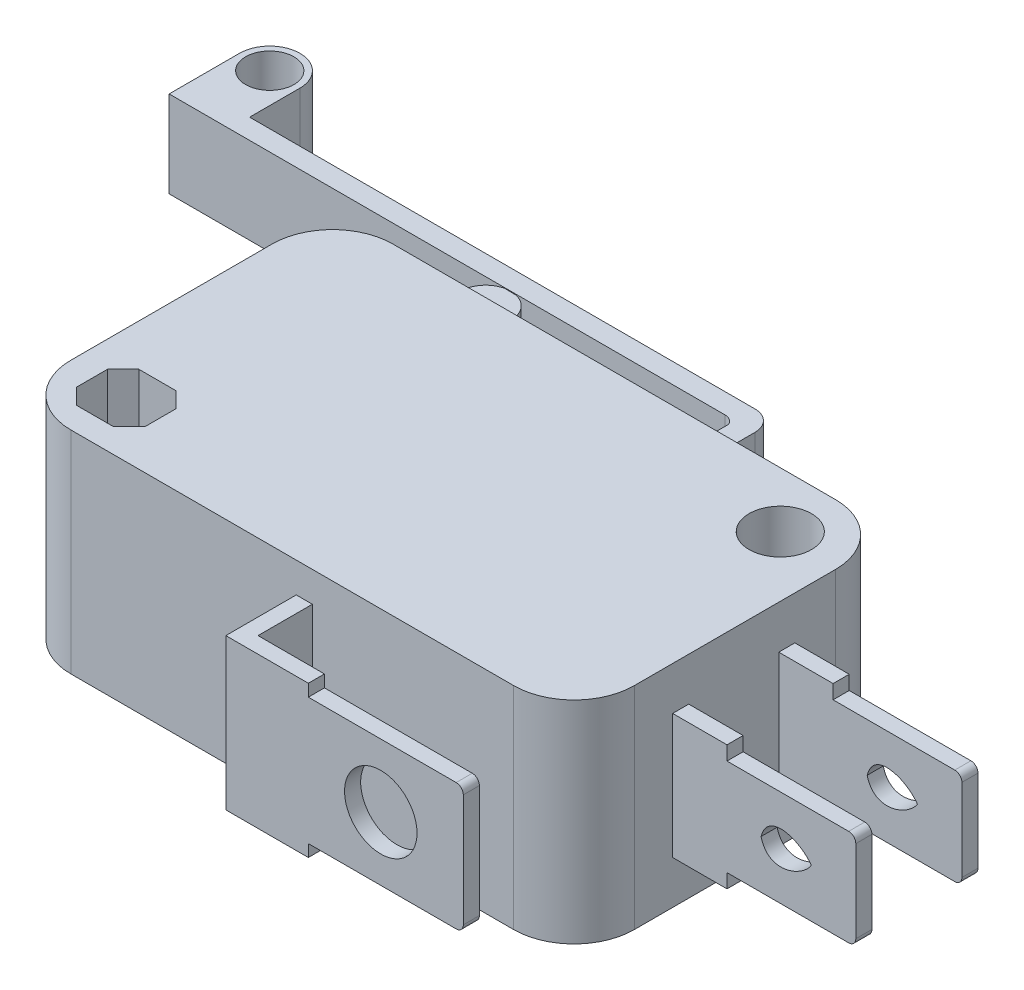
SolidWorks part; units mm, degrees
ref_plane "Alzado" through (0, 0, 0) normal (0, 0, 1) x (1, 0, 0)
ref_plane "Planta" through (0, 0, 0) normal (0, 1, 0) x (1, 0, 0)
ref_plane "Vista lateral" through (0, 0, 0) normal (1, 0, 0) x (0, 0, -1)
sketch "Croquis1" plane through (0, 0, 0) normal (0, 1, 0) x (1, 0, 0)
  line L0 (3, 0) -> (25, 0)
  line L1 (0, 3) -> (0, 13)
  line L2 (1.3, 3.525) -> (2.075, 4.3)
  line L3 (4.7, 3.525) -> (3.925, 4.3)
  line L4 (1.3, 1.975) -> (2.075, 1.2)
  line L5 (1.3, 2.75) -> (1.3, 3.525)
  line L6 (2.075, 4.3) -> (3.925, 4.3)
  line L7 (4.7, 3.525) -> (4.7, 1.975)
  line L8 (3.925, 1.2) -> (2.075, 1.2)
  line L9 (1.3, 1.975) -> (1.3, 2.75)
  line L10 (3.925, 1.2) -> (4.7, 1.975)
  line L13 (3, 16) -> (25, 16)
  line L15 (28, 13) -> (28, 3)
  arc A0 (0, 3) -> (3, 0) centre (3, 3) ccw
  circle A1 centre (25, 13.25) radius 1.55
  arc A2 (28, 13) -> (25, 16) centre (25, 13) ccw
  arc A3 (3, 16) -> (0, 13) centre (3, 13) ccw
  arc A4 (25, 0) -> (28, 3) centre (25, 3) ccw
extrude "Saliente-Extruir1" add sketch "Croquis1" along normal blind 10.5
sketch3d "Croquis3D1" plane through (0, 0, 0) normal (0, 0, 1) x (1, 0, 0)
  dimension "D1" = 3.1
sketch "Croquis2" plane through (0, 3.1, 0) normal (0, 1, 0) x (1, 0, 0)
  line L0 (-12.1172, 20) -> (15.5028, 20)
  line L1 (25, 16) -> (3, 16) construction
  line L2 (17, 16) -> (17, 20)
  line L3 (16, 21) -> (-9.1172, 21)
  line L5 (-12.1172, 21) -> (-12.1172, 20)
  line L9 (17, 16) -> (16, 16)
  line L10 (16, 16) -> (16, 19.6904)
  line L12 (-12.1172, 21) -> (-12.1172, 23.5)
  line L14 (-9.1172, 23.5) -> (-9.1172, 21)
  arc A0 (17, 20) -> (16, 21) centre (16, 20) ccw
  arc A1 (15.5028, 20) -> (16, 19.6904) centre (15.5028, 19.4459) cw
  arc A2 (-12.1172, 23.5) -> (-9.1172, 23.5) centre (-10.6172, 23.5) cw
  circle A3 centre (-10.6172, 23.5) radius 1.2
extrude "Saliente-Extruir2" add sketch "Croquis2" along normal blind 4.3
sketch "Croquis3" plane through (0, 3.1, 0) normal (0, 1, 0) x (1, 0, 0)
  line L0 (4.5799, 19.9682) -> (5.1781, 19.9589)
  line L1 (25, 16) -> (3, 16) construction
  line L3 (6.1101, 18.75) -> (6.1101, 16)
  line L4 (6.1101, 16) -> (3.6101, 16)
  line L5 (3.6101, 16) -> (3.6101, 18.75)
  arc A0 (3.6101, 18.75) -> (4.5799, 19.9682) centre (4.8601, 18.75) cw
  arc A1 (5.1781, 19.9589) -> (6.1101, 18.75) centre (4.8601, 18.75) cw
extrude "Saliente-Extruir6" add sketch "Croquis3" along normal blind 4.3
sketch3d "Croquis3D2" plane through (0, 0, 0) normal (0, 0, 1) x (1, 0, 0)
  dimension "D1" = 1.5
sketch "Croquis4" plane through (0, 1.5, 0) normal (0, 1, 0) x (1, 0, 0)
  line L1 (3, 0) -> (25, 0) construction
  line L2 (15, 0) -> (15, -2.7)
  line L3 (15, -3.5) -> (26, -3.5)
  line L4 (15, -3.5) -> (14.2, -3.5)
  line L5 (14.2, -3.5) -> (14.2, 0)
  line L6 (14.2, 0) -> (15, 0)
  line L7 (26, -3.5) -> (26, -2.7)
  line L8 (26, -2.7) -> (15, -2.7)
extrude "Saliente-Extruir7" add sketch "Croquis4" along normal blind 7.5
sketch "Croquis5" plane through (0, 0, 3.5) normal (0, 0, 1) x (1, 0, 0)
  line L0 (26, 1.5) -> (18.3, 1.5)
  line L1 (18.3, 1.5) -> (18.3, 2.1)
  line L2 (18.3, 2.1) -> (25.6464, 2.1)
  line L4 (26, 2.4536) -> (26, 8.0464)
  line L5 (25.6464, 8.4) -> (18.3, 8.4)
  line L6 (18.3, 8.4) -> (18.3, 9)
  line L7 (14.2, 9) -> (26, 9) construction
  line L8 (18.3, 9) -> (27.2932, 9)
  line L9 (27.2932, 9) -> (27.2932, 1.5)
  line L10 (27.2932, 1.5) -> (26, 1.5)
  arc A0 (25.6464, 2.1) -> (26, 2.4536) centre (25.6464, 2.4536) ccw
  arc A1 (26, 8.0464) -> (25.6464, 8.4) centre (25.6464, 8.0464) ccw
  circle A2 centre (21.9, 5.25) radius 1.8
extrude "Cortar-Extruir1" cut sketch "Croquis5" against normal blind 1.5
sketch3d "Croquis3D3" plane through (0, 0, 0) normal (0, 0, 1) x (1, 0, 0)
  dimension "D1" = 2.15
sketch "Croquis6" plane through (0, 2.15, 0) normal (0, 1, 0) x (1, 0, 0)
  line L0 (28, 10.974) -> (37.1, 10.974)
  line L1 (28, 3) -> (28, 13) construction
  line L2 (37.1, 10.974) -> (37.1, 10.174)
  line L3 (37.1, 10.174) -> (28, 10.174)
  line L4 (28, 10.174) -> (28, 10.974)
  line L5 (28, 5.7016) -> (37.1, 5.7016)
  line L6 (37.1, 5.7016) -> (37.1, 4.9016)
  line L7 (37.1, 4.9016) -> (28, 4.9016)
  line L8 (28, 4.9016) -> (28, 5.7016)
extrude "Saliente-Extruir8" add sketch "Croquis6" along normal blind 6.2
sketch "Croquis7" plane through (0, 0, -10.974) normal (0, 0, -1) x (-1, 0, 0)
  line L0 (-37.1, 2.15) -> (-30.7, 2.15)
  line L2 (-37.1, 2.15) -> (-28, 2.15) construction
  line L3 (-30.7, 2.15) -> (-30.7, 2.85)
  line L4 (-30.7, 2.85) -> (-36.7464, 2.85)
  line L6 (-37.1, 3.2036) -> (-37.1, 7.2964)
  line L7 (-36.7464, 7.65) -> (-30.7, 7.65)
  line L8 (-30.7, 7.65) -> (-30.7, 8.35)
  line L9 (-37.1, 8.35) -> (-28, 8.35) construction
  line L10 (-30.7, 8.35) -> (-37.1, 8.35)
  line L11 (-37.1, 8.35) -> (-38.5965, 8.35)
  line L12 (-38.5965, 8.35) -> (-38.5965, 2.85)
  line L13 (-38.5965, 2.85) -> (-38.5965, 2.15)
  line L14 (-38.5965, 2.15) -> (-37.1, 2.15)
  arc A0 (-36.7464, 7.65) -> (-37.1, 7.2964) centre (-36.7464, 7.2964) ccw
  arc A1 (-37.1, 3.2036) -> (-36.7464, 2.85) centre (-36.7464, 3.2036) ccw
  spline S1 degree 3 poles (-32.393, 5.25) (-32.7433, 3.8738) (-34.3822, 4.4793) (-34.893, 5.25) knots 0 0 0 0 1 1 1 1
  spline S2 degree 3 poles (-32.393, 5.25) (-32.7433, 6.6262) (-34.3822, 6.0207) (-34.893, 5.25) knots 0 0 0 0 1 1 1 1
extrude "Cortar-Extruir2" cut sketch "Croquis7" against normal blind 7.2
